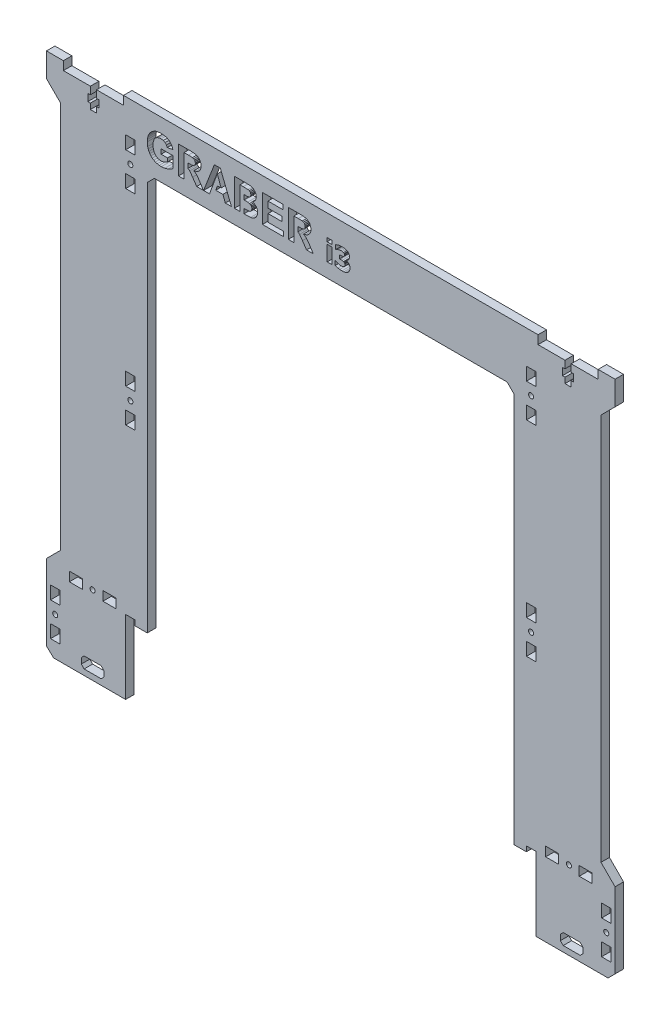
SolidWorks part; units mm, degrees
ref_plane "Plano frontal" through (0, 0, 0) normal (0, 0, 1) x (1, 0, 0)
ref_plane "Plano superior" through (0, 0, 0) normal (0, 1, 0) x (1, 0, 0)
ref_plane "Plano direito" through (0, 0, 0) normal (1, 0, 0) x (0, 0, -1)
sketch "Model" plane through (0, 0, 0) normal (0, 0, 1) x (1, 0, 0)
  line L0 (370.4961, 89.6431) -> (361.8461, 89.6431)
  line L1 (377.2461, 41.1432) -> (377.6461, 41.1339)
  line L2 (86.4962, 41.1432) -> (86.4962, 93.3339)
  line L3 (86.4962, 93.3339) -> (93.1962, 93.3339)
  line L4 (35.3962, 41.1339) -> (30.3962, 45.9422)
  line L5 (433.346, 46.1339) -> (428.346, 41.1339)
  line L6 (101.8462, 366.1338) -> (106.8462, 371.1338)
  line L7 (106.8462, 371.1338) -> (356.8461, 371.1338)
  line L8 (356.8461, 371.1338) -> (361.8461, 366.1338)
  line L9 (361.8461, 366.1338) -> (361.8461, 89.6431)
  line L10 (402.2461, 405.0338) -> (421.346, 405.0338)
  line L11 (421.346, 405.0338) -> (421.346, 411.1338)
  line L12 (59.6962, 399.7338) -> (59.6962, 394.6338)
  line L13 (65.8962, 405.0338) -> (84.9962, 405.0338)
  line L14 (397.8461, 399.7338) -> (396.0461, 399.7338)
  line L15 (404.0461, 399.7338) -> (402.2461, 399.7338)
  line L16 (421.346, 411.1338) -> (433.346, 411.1338)
  line L17 (84.9962, 405.0338) -> (84.9962, 411.1338)
  line L18 (397.8461, 394.6338) -> (397.8461, 390.6838)
  line L19 (402.2461, 390.6838) -> (402.2461, 394.6338)
  line L20 (396.0461, 399.7338) -> (396.0461, 394.6338)
  line L21 (378.7461, 411.1338) -> (378.7461, 405.0338)
  line L22 (378.7461, 405.0338) -> (397.8461, 405.0338)
  line L23 (396.0461, 394.6338) -> (397.8461, 394.6338)
  line L24 (397.8461, 390.6838) -> (402.2461, 390.6838)
  line L25 (402.2461, 394.6338) -> (404.0461, 394.6338)
  line L26 (397.8461, 405.0338) -> (397.8461, 399.7338)
  line L27 (402.2461, 399.7338) -> (402.2461, 405.0338)
  line L28 (404.0461, 394.6338) -> (404.0461, 399.7338)
  line L29 (433.346, 411.1338) -> (433.346, 394.1338)
  line L30 (428.346, 41.1339) -> (377.6461, 41.1339)
  line L31 (67.6962, 399.7338) -> (65.8962, 399.7338)
  line L32 (61.4962, 405.0338) -> (61.4962, 399.7338)
  line L33 (65.8962, 394.6338) -> (67.6962, 394.6338)
  line L34 (65.8962, 399.7338) -> (65.8962, 405.0338)
  line L35 (61.4962, 390.6838) -> (65.8962, 390.6838)
  line L36 (67.6962, 394.6338) -> (67.6962, 399.7338)
  line L37 (61.4962, 394.6338) -> (61.4962, 390.6838)
  line L38 (65.8962, 390.6838) -> (65.8962, 394.6338)
  line L39 (61.4962, 399.7338) -> (59.6962, 399.7338)
  line L40 (59.6962, 394.6338) -> (61.4962, 394.6338)
  line L41 (30.3962, 45.9422) -> (30.3962, 99.6339)
  line L42 (30.3962, 411.1338) -> (42.3962, 411.1338)
  line L43 (42.3962, 405.0338) -> (61.4962, 405.0338)
  line L44 (42.3962, 411.1338) -> (42.3962, 405.0338)
  line L45 (84.9962, 411.1338) -> (378.7461, 411.1338)
  line L46 (93.1962, 93.3339) -> (93.1962, 89.6431)
  line L47 (101.8462, 89.6431) -> (101.8462, 366.1338)
  line L48 (93.1962, 89.6431) -> (101.8462, 89.6431)
  line L49 (377.2461, 41.1432) -> (377.2461, 93.3339)
  line L50 (377.2461, 93.3339) -> (370.4961, 93.3339)
  line L51 (370.4961, 93.3339) -> (370.4961, 89.6431)
  line L52 (86.0462, 41.1339) -> (35.3962, 41.1339)
  line L53 (86.4962, 41.1432) -> (86.0462, 41.1339)
  line L54 (30.3962, 99.6339) -> (40.3962, 109.6339)
  line L55 (30.3962, 394.1338) -> (30.3962, 411.1338)
  line L56 (30.3962, 394.1338) -> (40.3962, 384.1338)
  line L57 (40.3962, 384.1338) -> (40.3962, 109.6339)
  line L58 (433.346, 99.6339) -> (433.346, 46.1339)
  line L59 (433.346, 99.6339) -> (423.346, 109.6339)
  line L60 (423.346, 109.6339) -> (423.346, 384.1338)
  line L61 (423.346, 384.1338) -> (433.346, 394.1338)
  line L62 (55.7962, 93.3838) -> (55.7962, 99.9838)
  line L63 (70.3962, 99.9838) -> (70.3962, 93.3838)
  line L64 (70.3962, 93.3838) -> (79.5962, 93.3838)
  line L65 (430.3961, 51.8839) -> (430.3961, 61.0839)
  line L66 (86.5462, 363.928) -> (86.5462, 354.728)
  line L67 (93.1462, 378.528) -> (93.1462, 387.728)
  line L68 (139.995, 395.2854) -> (139.9137, 394.227)
  line L69 (139.9137, 394.227) -> (139.6698, 393.2649)
  line L70 (139.6698, 393.2649) -> (139.2632, 392.3993)
  line L71 (139.2632, 392.3993) -> (138.6939, 391.6301)
  line L72 (93.1462, 387.728) -> (86.5462, 387.728)
  line L73 (86.5462, 387.728) -> (86.5462, 378.528)
  line L74 (86.5462, 378.528) -> (93.1462, 378.528)
  line L75 (86.5462, 354.728) -> (93.1462, 354.728)
  line L76 (93.1462, 354.728) -> (93.1462, 363.928)
  line L77 (93.1462, 363.928) -> (86.5462, 363.928)
  line L78 (93.1462, 242.6431) -> (86.5462, 242.6431)
  line L79 (86.5462, 242.6431) -> (86.5462, 233.4431)
  line L80 (86.5462, 233.4431) -> (93.1462, 233.4431)
  line L81 (86.5462, 209.6431) -> (93.1462, 209.6431)
  line L82 (93.1462, 209.6431) -> (93.1462, 218.8431)
  line L83 (93.1462, 218.8431) -> (86.5462, 218.8431)
  line L84 (86.5462, 218.8431) -> (86.5462, 209.6431)
  line L85 (33.2962, 51.8839) -> (39.8962, 51.8839)
  line L86 (39.8962, 75.6839) -> (39.8962, 84.8838)
  line L87 (39.8962, 84.8838) -> (33.2962, 84.8838)
  line L88 (33.2962, 84.8838) -> (33.2962, 75.6839)
  line L89 (33.2962, 75.6839) -> (39.8962, 75.6839)
  line L90 (55.7962, 99.9838) -> (46.5962, 99.9838)
  line L91 (46.5962, 99.9838) -> (46.5962, 93.3838)
  line L92 (46.5962, 93.3838) -> (55.7962, 93.3838)
  line L93 (384.1461, 99.9838) -> (384.1461, 93.3838)
  line L94 (384.1461, 93.3838) -> (393.3461, 93.3838)
  line L95 (393.3461, 93.3838) -> (393.3461, 99.9838)
  line L96 (393.3461, 99.9838) -> (384.1461, 99.9838)
  line L97 (407.9461, 93.3838) -> (417.146, 93.3838)
  line L98 (79.5962, 93.3838) -> (79.5962, 99.9838)
  line L99 (417.146, 93.3838) -> (417.146, 99.9838)
  line L100 (417.146, 99.9838) -> (407.9461, 99.9838)
  line L101 (407.9461, 99.9838) -> (407.9461, 93.3838)
  line L102 (430.3961, 84.8838) -> (423.7961, 84.8838)
  line L103 (39.8962, 61.0839) -> (33.2962, 61.0839)
  line L104 (33.2962, 61.0839) -> (33.2962, 51.8839)
  line L105 (93.1462, 233.4431) -> (93.1462, 242.6431)
  line L106 (370.5461, 218.8431) -> (370.5461, 209.6431)
  line L107 (377.1461, 242.6431) -> (370.5461, 242.6431)
  line L108 (370.5461, 387.728) -> (370.5461, 378.528)
  line L109 (370.5461, 378.528) -> (377.1461, 378.528)
  line L110 (377.1461, 387.728) -> (370.5461, 387.728)
  line L111 (377.1461, 233.4431) -> (377.1461, 242.6431)
  line L112 (377.1461, 218.8431) -> (370.5461, 218.8431)
  line L113 (370.5461, 233.4431) -> (377.1461, 233.4431)
  line L114 (370.5461, 209.6431) -> (377.1461, 209.6431)
  line L115 (370.5461, 242.6431) -> (370.5461, 233.4431)
  line L116 (377.1461, 209.6431) -> (377.1461, 218.8431)
  line L117 (39.8962, 51.8839) -> (39.8962, 61.0839)
  line L118 (79.5962, 99.9838) -> (70.3962, 99.9838)
  line L119 (104.7201, 398.602) -> (105.737, 399.4479)
  line L120 (105.737, 399.4479) -> (106.9032, 400.1546)
  line L121 (106.9032, 400.1546) -> (107.9067, 400.583)
  line L122 (107.9067, 400.583) -> (109.0259, 400.889)
  line L123 (109.0259, 400.889) -> (111.6114, 401.1338)
  line L124 (111.6114, 401.1338) -> (113.3422, 401.0378)
  line L125 (113.3422, 401.0378) -> (114.8726, 400.7498)
  line L126 (114.8726, 400.7498) -> (116.2027, 400.2699)
  line L127 (116.2027, 400.2699) -> (117.3324, 399.5979)
  line L128 (117.3324, 399.5979) -> (118.2701, 398.7566)
  line L129 (118.2701, 398.7566) -> (119.0242, 397.7686)
  line L130 (119.0242, 397.7686) -> (119.5947, 396.6339)
  line L131 (119.5947, 396.6339) -> (119.9816, 395.3525)
  line L132 (119.9816, 395.3525) -> (116.038, 394.6147)
  line L133 (116.038, 394.6147) -> (115.4394, 395.9108)
  line L134 (115.4394, 395.9108) -> (114.4753, 396.9018)
  line L135 (114.4753, 396.9018) -> (113.1859, 397.5305)
  line L136 (113.1859, 397.5305) -> (111.6114, 397.7401)
  line L137 (111.6114, 397.7401) -> (110.3769, 397.637)
  line L138 (110.3769, 397.637) -> (109.2757, 397.3276)
  line L139 (109.2757, 397.3276) -> (108.3078, 396.812)
  line L140 (108.3078, 396.812) -> (107.4733, 396.0902)
  line L141 (107.4733, 396.0902) -> (106.8013, 395.1655)
  line L142 (106.8013, 395.1655) -> (106.3213, 394.0413)
  line L143 (106.3213, 394.0413) -> (106.0334, 392.7175)
  line L144 (106.0334, 392.7175) -> (105.9374, 391.1942)
  line L145 (105.9374, 391.1942) -> (106.0346, 389.5531)
  line L146 (106.0346, 389.5531) -> (106.3264, 388.1308)
  line L147 (106.3264, 388.1308) -> (106.8126, 386.9273)
  line L148 (106.8126, 386.9273) -> (107.4934, 385.9427)
  line L149 (107.4934, 385.9427) -> (108.3317, 385.1768)
  line L150 (108.3317, 385.1768) -> (109.2908, 384.6298)
  line L151 (109.2908, 384.6298) -> (110.3706, 384.3016)
  line L152 (110.3706, 384.3016) -> (111.5712, 384.1922)
  line L153 (111.5712, 384.1922) -> (112.8203, 384.3146)
  line L154 (112.8203, 384.3146) -> (114.0728, 384.6818)
  line L155 (114.0728, 384.6818) -> (115.2382, 385.2233)
  line L156 (115.2382, 385.2233) -> (116.2258, 385.8689)
  line L157 (116.2258, 385.8689) -> (116.2258, 388.3639)
  line L158 (116.2258, 388.3639) -> (111.6785, 388.3639)
  line L159 (111.6785, 388.3639) -> (111.6785, 391.6771)
  line L160 (111.6785, 391.6771) -> (120.2365, 391.6771)
  line L161 (120.2365, 391.6771) -> (120.2365, 383.8434)
  line L162 (120.2365, 383.8434) -> (118.709, 382.7083)
  line L163 (118.709, 382.7083) -> (116.6215, 381.7173)
  line L164 (116.6215, 381.7173) -> (114.2388, 381.0282)
  line L165 (114.2388, 381.0282) -> (111.826, 380.7985)
  line L166 (111.826, 380.7985) -> (110.3329, 380.8794)
  line L167 (110.3329, 380.8794) -> (108.9387, 381.1221)
  line L168 (108.9387, 381.1221) -> (107.6434, 381.5266)
  line L169 (107.6434, 381.5266) -> (106.4471, 382.0929)
  line L170 (106.4471, 382.0929) -> (105.3715, 382.8097)
  line L171 (105.3715, 382.8097) -> (104.4384, 383.6657)
  line L172 (104.4384, 383.6657) -> (103.6478, 384.6608)
  line L173 (103.6478, 384.6608) -> (102.9997, 385.7951)
  line L174 (102.9997, 385.7951) -> (102.495, 387.0254)
  line L175 (102.495, 387.0254) -> (102.1346, 388.3085)
  line L176 (102.1346, 388.3085) -> (101.8462, 391.0332)
  line L177 (101.8462, 391.0332) -> (101.9266, 392.5263)
  line L178 (101.9266, 392.5263) -> (102.1681, 393.9339)
  line L179 (102.1681, 393.9339) -> (102.5705, 395.256)
  line L180 (102.5705, 395.256) -> (103.1339, 396.4926)
  line L181 (103.1339, 396.4926) -> (103.8524, 397.6169)
  line L182 (103.8524, 397.6169) -> (104.7201, 398.602)
  line L183 (175.0722, 381.2679) -> (170.3604, 381.136)
  line L184 (170.3604, 384.447) -> (170.3604, 381.136)
  line L185 (170.3604, 384.447) -> (171.2358, 384.447)
  line L186 (171.2358, 384.447) -> (173.9588, 384.5677)
  line L187 (173.9588, 384.5677) -> (174.762, 384.8444)
  line L188 (174.762, 384.8444) -> (175.4008, 385.3525)
  line L189 (175.4008, 385.3525) -> (175.8183, 386.0818)
  line L190 (175.8183, 386.0818) -> (175.9575, 387.0225)
  line L191 (175.9575, 387.0225) -> (175.8502, 387.8407)
  line L192 (175.8502, 387.8407) -> (175.5282, 388.5248)
  line L193 (175.5282, 388.5248) -> (175.0034, 389.058)
  line L194 (175.0034, 389.058) -> (174.2875, 389.4235)
  line L195 (174.2875, 389.4235) -> (173.0014, 389.6348)
  line L196 (173.0014, 389.6348) -> (170.7663, 389.7052)
  line L197 (170.7663, 389.7052) -> (170.3604, 389.7052)
  line L198 (170.3604, 389.7052) -> (170.3604, 392.9828)
  line L199 (170.3604, 392.9828) -> (173.0467, 393.0453)
  line L200 (173.0467, 393.0453) -> (173.9572, 393.2817)
  line L201 (173.9572, 393.2817) -> (174.6496, 393.7495)
  line L202 (174.6496, 393.7495) -> (175.0873, 394.4252)
  line L203 (175.0873, 394.4252) -> (175.2331, 395.2854)
  line L204 (175.2331, 395.2854) -> (175.1074, 396.112)
  line L205 (175.1074, 396.112) -> (174.7301, 396.7676)
  line L206 (174.7301, 396.7676) -> (174.1047, 397.2254)
  line L207 (174.1047, 397.2254) -> (173.2345, 397.4584)
  line L208 (173.2345, 397.4584) -> (169.8408, 397.5255)
  line L209 (169.8408, 397.5255) -> (167.5604, 397.5255)
  line L210 (167.5604, 397.5255) -> (167.5604, 381.1338)
  line L211 (167.5604, 381.1338) -> (163.59, 381.1338)
  line L212 (163.59, 381.1338) -> (163.59, 400.7985)
  line L213 (163.59, 400.7985) -> (171.4504, 400.7985)
  line L214 (171.4504, 400.7985) -> (174.9313, 400.604)
  line L215 (174.9313, 400.604) -> (176.0179, 400.3038)
  line L216 (176.0179, 400.3038) -> (176.9836, 399.7924)
  line L217 (176.9836, 399.7924) -> (177.8136, 399.0731)
  line L218 (177.8136, 399.0731) -> (178.4927, 398.1492)
  line L219 (178.4927, 398.1492) -> (178.9454, 397.061)
  line L220 (178.9454, 397.061) -> (179.0963, 395.8488)
  line L221 (179.0963, 395.8488) -> (178.9102, 394.5242)
  line L222 (178.9102, 394.5242) -> (178.3519, 393.3136)
  line L223 (178.3519, 393.3136) -> (177.4749, 392.3042)
  line L224 (177.4749, 392.3042) -> (176.3331, 391.5832)
  line L225 (176.3331, 391.5832) -> (177.9226, 390.8756)
  line L226 (177.9226, 390.8756) -> (179.0963, 389.7991)
  line L227 (179.0963, 389.7991) -> (179.8207, 388.4276)
  line L228 (179.8207, 388.4276) -> (180.0621, 386.8347)
  line L229 (180.0621, 386.8347) -> (179.9062, 385.5117)
  line L230 (179.9062, 385.5117) -> (179.4384, 384.2257)
  line L231 (179.4384, 384.2257) -> (178.7006, 383.0855)
  line L232 (178.7006, 383.0855) -> (177.7348, 382.2002)
  line L233 (177.7348, 382.2002) -> (176.5293, 381.5882)
  line L234 (176.5293, 381.5882) -> (175.0722, 381.2679)
  line L235 (209.1399, 388.8065) -> (208.5262, 389.1217)
  line L236 (208.5227, 392.4819) -> (208.5262, 389.1217)
  line L237 (208.5227, 392.4819) -> (208.6604, 392.4819)
  line L238 (208.6604, 392.4819) -> (210.981, 392.5423)
  line L239 (210.981, 392.5423) -> (212.2284, 392.7233)
  line L240 (212.2284, 392.7233) -> (212.8623, 393.052)
  line L241 (212.8623, 393.052) -> (213.3418, 393.555)
  line L242 (213.3418, 393.555) -> (213.6436, 394.219)
  line L243 (213.6436, 394.219) -> (213.7442, 395.0305)
  line L244 (213.7442, 395.0305) -> (213.6117, 395.9276)
  line L245 (213.6117, 395.9276) -> (213.2144, 396.6335)
  line L246 (213.2144, 396.6335) -> (212.5755, 397.1315)
  line L247 (212.5755, 397.1315) -> (211.7187, 397.4048)
  line L248 (211.7187, 397.4048) -> (208.8213, 397.4718)
  line L249 (208.8213, 397.4718) -> (205.7227, 397.4718)
  line L250 (205.7227, 397.4718) -> (205.7227, 381.1338)
  line L251 (205.7227, 381.1338) -> (201.7523, 381.1338)
  line L252 (201.7523, 381.1338) -> (201.7523, 400.7985)
  line L253 (201.7523, 400.7985) -> (210.1091, 400.7985)
  line L254 (210.1091, 400.7985) -> (212.8304, 400.666)
  line L255 (212.8304, 400.666) -> (214.6899, 400.2686)
  line L256 (214.6899, 400.2686) -> (215.9759, 399.5325)
  line L257 (215.9759, 399.5325) -> (216.9769, 398.384)
  line L258 (216.9769, 398.384) -> (217.6208, 396.9319)
  line L259 (217.6208, 396.9319) -> (217.8354, 395.2854)
  line L260 (217.8354, 395.2854) -> (217.7541, 394.227)
  line L261 (217.7541, 394.227) -> (217.5101, 393.2649)
  line L262 (217.5101, 393.2649) -> (217.1035, 392.3993)
  line L263 (217.1035, 392.3993) -> (216.5343, 391.6301)
  line L264 (216.5343, 391.6301) -> (215.8032, 390.9758)
  line L265 (215.8032, 390.9758) -> (214.9112, 390.4547)
  line L266 (214.9112, 390.4547) -> (213.8582, 390.067)
  line L267 (213.8582, 390.067) -> (212.6443, 389.8125)
  line L268 (212.6443, 389.8125) -> (213.8197, 389.0245)
  line L269 (213.8197, 389.0245) -> (214.7704, 388.1626)
  line L270 (214.7704, 388.1626) -> (215.7546, 386.9152)
  line L271 (215.7546, 386.9152) -> (217.0306, 384.9702)
  line L272 (217.0306, 384.9702) -> (219.4317, 381.1338)
  line L273 (219.4317, 381.1338) -> (214.6832, 381.1338)
  line L274 (214.6832, 381.1338) -> (211.8126, 385.4128)
  line L275 (211.8126, 385.4128) -> (209.7201, 388.3035)
  line L276 (209.7201, 388.3035) -> (209.1399, 388.8065)
  line L277 (150.3724, 385.6006) -> (151.5931, 388.9138)
  line L278 (151.5931, 388.9138) -> (154.16, 388.9138)
  line L279 (154.16, 388.9138) -> (151.4504, 396.2109)
  line L280 (151.4504, 396.2109) -> (145.9508, 381.1338)
  line L281 (145.9508, 381.1338) -> (141.7388, 381.1338)
  line L282 (141.7388, 381.1338) -> (149.3981, 400.7985)
  line L283 (149.3981, 400.7985) -> (153.5967, 400.7985)
  line L284 (153.5967, 400.7985) -> (161.4706, 381.1338)
  line L285 (161.4706, 381.1338) -> (157.1513, 381.1338)
  line L286 (157.1513, 381.1338) -> (155.4344, 385.6006)
  line L287 (155.4344, 385.6006) -> (150.3724, 385.6006)
  line L288 (423.7961, 51.8839) -> (430.3961, 51.8839)
  line L289 (423.7961, 61.0839) -> (423.7961, 51.8839)
  line L290 (430.3961, 61.0839) -> (423.7961, 61.0839)
  line L291 (198.372, 381.1338) -> (183.4156, 381.1338)
  line L292 (183.4156, 381.1338) -> (183.4156, 400.7985)
  line L293 (183.4156, 400.7985) -> (197.9964, 400.7985)
  line L294 (197.9964, 400.7985) -> (197.9964, 397.4718)
  line L295 (197.9964, 397.4718) -> (187.3861, 397.4718)
  line L296 (187.3861, 397.4718) -> (187.3861, 393.1123)
  line L297 (187.3861, 393.1123) -> (197.2586, 393.1123)
  line L298 (197.2586, 393.1123) -> (197.2586, 389.7991)
  line L299 (197.2586, 389.7991) -> (187.3861, 389.7991)
  line L300 (187.3861, 389.7991) -> (187.3861, 384.447)
  line L301 (187.3861, 384.447) -> (198.372, 384.447)
  line L302 (198.372, 384.447) -> (198.372, 381.1338)
  line L303 (430.3961, 75.6839) -> (430.3961, 84.8838)
  line L304 (423.7961, 75.6839) -> (430.3961, 75.6839)
  line L305 (423.7961, 84.8838) -> (423.7961, 75.6839)
  line L306 (377.1461, 378.528) -> (377.1461, 387.728)
  line L307 (377.1461, 363.928) -> (370.5461, 363.928)
  line L308 (377.1461, 354.728) -> (377.1461, 363.928)
  line L309 (370.5461, 354.728) -> (377.1461, 354.728)
  line L310 (370.5461, 363.928) -> (370.5461, 354.728)
  line L311 (57.0982, 53.1707) -> (69.0942, 53.1707)
  line L312 (71.0942, 51.1707) -> (69.0942, 53.1707)
  line L313 (71.0942, 47.1707) -> (71.0942, 51.1707)
  line L314 (69.0942, 45.1707) -> (71.0942, 47.1707)
  line L315 (57.0982, 45.1707) -> (69.0942, 45.1707)
  line L316 (55.0982, 47.1707) -> (57.0982, 45.1707)
  line L317 (55.0982, 51.1707) -> (55.0982, 47.1707)
  line L318 (55.0982, 51.1707) -> (57.0982, 53.1707)
  line L319 (410.594, 51.1707) -> (410.594, 47.1707)
  line L320 (408.594, 45.1707) -> (410.594, 47.1707)
  line L321 (396.5981, 45.1707) -> (408.594, 45.1707)
  line L322 (394.5981, 47.1707) -> (396.5981, 45.1707)
  line L323 (394.5981, 47.1707) -> (394.5981, 51.1707)
  line L324 (396.5981, 53.1707) -> (394.5981, 51.1707)
  line L325 (396.5981, 53.1707) -> (408.594, 53.1707)
  line L326 (410.594, 51.1707) -> (408.594, 53.1707)
  line L327 (131.2995, 388.8065) -> (130.6859, 389.1217)
  line L328 (130.6859, 389.1217) -> (130.6859, 392.4819)
  line L329 (130.6859, 392.4819) -> (130.82, 392.4819)
  line L330 (130.82, 392.4819) -> (133.1406, 392.5423)
  line L331 (133.1406, 392.5423) -> (134.3881, 392.7233)
  line L332 (134.3881, 392.7233) -> (135.0219, 393.052)
  line L333 (135.0219, 393.052) -> (135.5014, 393.555)
  line L334 (135.5014, 393.555) -> (135.8032, 394.219)
  line L335 (135.8032, 394.219) -> (135.9038, 395.0305)
  line L336 (135.9038, 395.0305) -> (135.7714, 395.9276)
  line L337 (135.7714, 395.9276) -> (135.374, 396.6335)
  line L338 (135.374, 396.6335) -> (134.7352, 397.1315)
  line L339 (134.7352, 397.1315) -> (133.8783, 397.4048)
  line L340 (133.8783, 397.4048) -> (130.981, 397.4718)
  line L341 (130.981, 397.4718) -> (127.8824, 397.4718)
  line L342 (127.8824, 397.4718) -> (127.8824, 381.1338)
  line L343 (127.8824, 381.1338) -> (123.9119, 381.1338)
  line L344 (123.9119, 381.1338) -> (123.9119, 400.7985)
  line L345 (123.9119, 400.7985) -> (132.2687, 400.7985)
  line L346 (132.2687, 400.7985) -> (134.99, 400.666)
  line L347 (134.99, 400.666) -> (136.8495, 400.2686)
  line L348 (136.8495, 400.2686) -> (138.1356, 399.5325)
  line L349 (138.1356, 399.5325) -> (139.1366, 398.384)
  line L350 (139.1366, 398.384) -> (139.7804, 396.9319)
  line L351 (139.7804, 396.9319) -> (139.995, 395.2854)
  line L352 (138.6939, 391.6301) -> (137.9629, 390.9758)
  line L353 (137.9629, 390.9758) -> (137.0708, 390.4547)
  line L354 (137.0708, 390.4547) -> (136.0179, 390.067)
  line L355 (136.0179, 390.067) -> (134.8039, 389.8125)
  line L356 (134.8039, 389.8125) -> (135.9793, 389.0245)
  line L357 (135.9793, 389.0245) -> (136.93, 388.1626)
  line L358 (136.93, 388.1626) -> (137.9142, 386.9152)
  line L359 (137.9142, 386.9152) -> (139.1902, 384.9702)
  line L360 (139.1902, 384.9702) -> (141.5913, 381.1338)
  line L361 (141.5913, 381.1338) -> (136.8428, 381.1338)
  line L362 (136.8428, 381.1338) -> (133.9722, 385.4128)
  line L363 (133.9722, 385.4128) -> (131.8797, 388.3035)
  line L364 (131.8797, 388.3035) -> (131.2995, 388.8065)
  line L365 (232.8025, 393.4231) -> (229.2584, 393.4231)
  line L366 (229.2584, 393.4231) -> (229.2584, 396.038)
  line L367 (229.2584, 396.038) -> (232.8025, 396.038)
  line L368 (232.8025, 396.038) -> (232.8025, 393.4231)
  line L369 (229.3542, 381.1338) -> (229.3542, 391.8905)
  line L370 (229.3542, 391.8905) -> (232.7067, 391.8905)
  line L371 (232.7067, 391.8905) -> (232.7067, 381.1338)
  line L372 (232.7067, 381.1338) -> (229.3542, 381.1338)
  line L373 (239.9289, 395.6932) -> (241.1179, 395.6381)
  line L374 (241.1179, 395.6381) -> (242.1368, 395.4729)
  line L375 (242.1368, 395.4729) -> (243.0025, 395.2023)
  line L376 (243.0025, 395.2023) -> (243.7316, 394.8311)
  line L377 (243.7316, 394.8311) -> (244.3686, 394.3199)
  line L378 (244.3686, 394.3199) -> (244.8236, 393.6865)
  line L379 (244.8236, 393.6865) -> (245.0966, 392.9477)
  line L380 (245.0966, 392.9477) -> (245.1876, 392.1204)
  line L381 (245.1876, 392.1204) -> (245.0116, 390.9794)
  line L382 (245.0116, 390.9794) -> (244.4835, 389.9892)
  line L383 (244.4835, 389.9892) -> (243.6682, 389.2361)
  line L384 (243.6682, 389.2361) -> (242.6301, 388.8062)
  line L385 (242.6301, 388.8062) -> (242.6301, 388.6721)
  line L386 (242.6301, 388.6721) -> (243.6215, 388.4135)
  line L387 (243.6215, 388.4135) -> (244.565, 387.8196)
  line L388 (244.565, 387.8196) -> (244.9589, 387.3922)
  line L389 (244.9589, 387.3922) -> (245.2786, 386.857)
  line L390 (245.2786, 386.857) -> (245.4905, 386.2116)
  line L391 (245.4905, 386.2116) -> (245.5611, 385.4537)
  line L392 (245.5611, 385.4537) -> (245.4641, 384.4552)
  line L393 (245.4641, 384.4552) -> (245.1732, 383.5476)
  line L394 (245.1732, 383.5476) -> (244.6955, 382.7502)
  line L395 (244.6955, 382.7502) -> (244.0381, 382.0821)
  line L396 (244.0381, 382.0821) -> (243.2156, 381.5493)
  line L397 (243.2156, 381.5493) -> (242.2613, 381.1578)
  line L398 (242.2613, 381.1578) -> (241.1299, 380.9171)
  line L399 (241.1299, 380.9171) -> (239.7757, 380.8369)
  line L400 (239.7757, 380.8369) -> (238.2276, 380.9063)
  line L401 (238.2276, 380.9063) -> (236.9165, 381.1147)
  line L402 (236.9165, 381.1147) -> (234.9768, 381.7373)
  line L403 (234.9768, 381.7373) -> (234.9768, 384.8311)
  line L404 (234.9768, 384.8311) -> (235.3217, 384.8311)
  line L405 (235.3217, 384.8311) -> (236.1753, 384.3666)
  line L406 (236.1753, 384.3666) -> (237.1655, 383.9691)
  line L407 (237.1655, 383.9691) -> (238.1773, 383.6961)
  line L408 (238.1773, 383.6961) -> (239.0956, 383.6051)
  line L409 (239.0956, 383.6051) -> (240.2211, 383.6961)
  line L410 (240.2211, 383.6961) -> (240.7802, 383.8409)
  line L411 (240.7802, 383.8409) -> (241.2412, 384.0936)
  line L412 (241.2412, 384.0936) -> (241.7632, 384.6827)
  line L413 (241.7632, 384.6827) -> (241.9105, 385.1053)
  line L414 (241.9105, 385.1053) -> (241.9596, 385.674)
  line L415 (241.9596, 385.674) -> (241.8901, 386.2332)
  line L416 (241.8901, 386.2332) -> (241.6818, 386.6463)
  line L417 (241.6818, 386.6463) -> (241.3585, 386.9396)
  line L418 (241.3585, 386.9396) -> (240.9443, 387.1396)
  line L419 (240.9443, 387.1396) -> (239.8427, 387.3215)
  line L420 (239.8427, 387.3215) -> (238.7125, 387.3407)
  line L421 (238.7125, 387.3407) -> (238.0994, 387.3407)
  line L422 (238.0994, 387.3407) -> (238.0994, 389.8503)
  line L423 (238.0994, 389.8503) -> (238.6646, 389.8503)
  line L424 (238.6646, 389.8503) -> (239.8619, 389.9078)
  line L425 (239.8619, 389.9078) -> (240.791, 390.1376)
  line L426 (240.791, 390.1376) -> (241.3897, 390.6453)
  line L427 (241.3897, 390.6453) -> (241.5513, 391.0284)
  line L428 (241.5513, 391.0284) -> (241.6052, 391.5265)
  line L429 (241.6052, 391.5265) -> (241.5549, 391.9181)
  line L430 (241.5549, 391.9181) -> (241.404, 392.2306)
  line L431 (241.404, 392.2306) -> (240.906, 392.6568)
  line L432 (240.906, 392.6568) -> (240.1014, 392.8867)
  line L433 (240.1014, 392.8867) -> (239.3159, 392.9442)
  line L434 (239.3159, 392.9442) -> (238.2431, 392.8196)
  line L435 (238.2431, 392.8196) -> (237.1799, 392.5035)
  line L436 (237.1799, 392.5035) -> (236.337, 392.106)
  line L437 (236.337, 392.106) -> (235.6856, 391.7373)
  line L438 (235.6856, 391.7373) -> (235.3887, 391.7373)
  line L439 (235.3887, 391.7373) -> (235.3887, 394.7928)
  line L440 (235.3887, 394.7928) -> (237.3763, 395.4011)
  line L441 (237.3763, 395.4011) -> (238.6394, 395.6202)
  line L442 (238.6394, 395.6202) -> (239.9289, 395.6932)
  circle A0 centre (427.0961, 68.3839) radius 1.8
  circle A1 centre (400.6461, 96.6838) radius 1.8
  circle A2 centre (373.8461, 226.1431) radius 1.8
  circle A3 centre (373.8461, 371.228) radius 1.8
  circle A4 centre (89.8462, 371.228) radius 1.8
  circle A5 centre (89.8462, 226.1431) radius 1.8
  circle A6 centre (63.0962, 96.6838) radius 1.8
  circle A7 centre (36.5962, 68.3839) radius 1.8
extrude "Ressalto-extrusão1" add sketch "Model" along normal blind 6
ref_plane "Plano1" through (427.0961, 0, 0) normal (1, 0, 0) x (0, 0, -1)
ref_plane "Plano2" through (36.5962, 0, 0) normal (-1, 0, 0) x (0, 0, 1)
ref_plane "Plano3" through (0, 68.3839, 0) normal (0, 1, 0) x (1, 0, 0)
ref_plane "Plano4" through (63.0962, 0, 0) normal (1, 0, 0) x (0, 0, -1)
ref_plane "Plano5" through (400.6461, 0, 0) normal (1, 0, 0) x (0, 0, -1)
